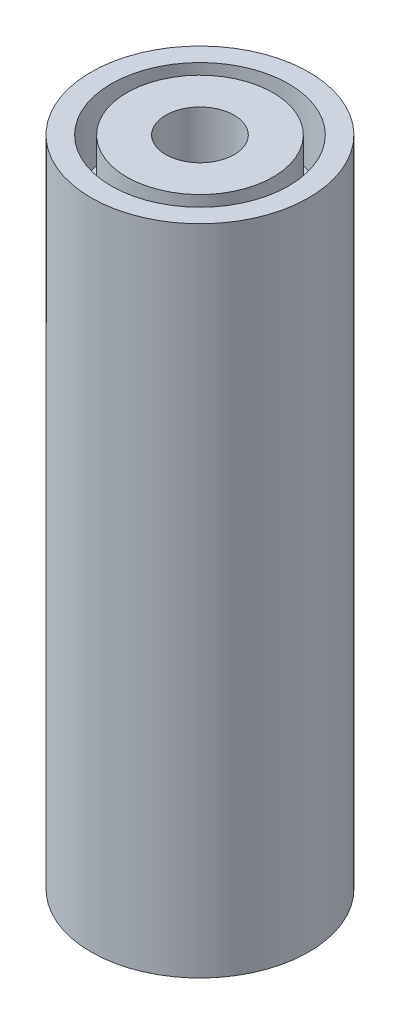
SolidWorks part; units mm, degrees
ref_plane "Plan de face" through (0, 0, 0) normal (0, 0, 1) x (1, 0, 0)
ref_plane "Plan de dessus" through (0, 0, 0) normal (0, 1, 0) x (1, 0, 0)
ref_plane "Plan de droite" through (0, 0, 0) normal (1, 0, 0) x (0, 0, -1)
sketch "Esquisse1" plane through (0, 0, 0) normal (0, 1, 0) x (1, 0, 0)
  circle A0 centre (0, 0) radius 1.1
  circle A1 centre (0, 0) radius 3.5
  dimension "D1" = 2.2
  dimension "D2" = 7
extrude "Boss.-Extru.2" add sketch "Esquisse1" along normal blind 21
sketch "Esquisse2" plane through (0, 21, 0) normal (0, 1, 0) x (1, 0, 0)
  circle A0 centre (0, 0) radius 2.35
  circle A1 centre (0, 0) radius 2.85
  dimension "D1" = 5.7
  dimension "D2" = 0.5
extrude "Enlèv. mat.-Extru.1" cut sketch "Esquisse2" against normal blind 2
